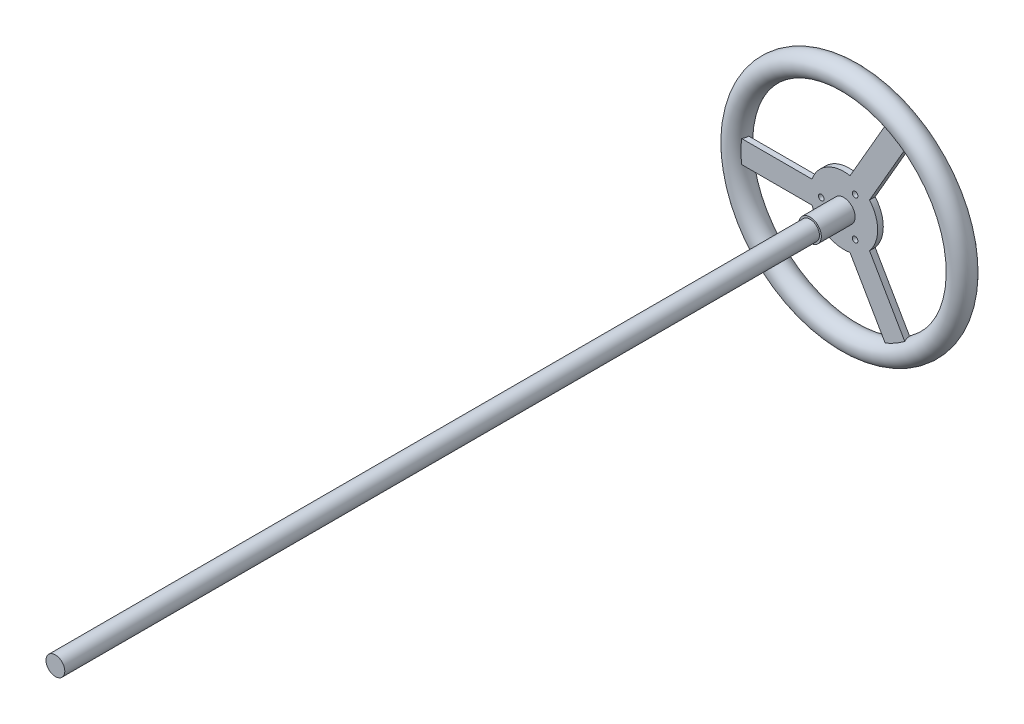
SolidWorks part; units mm, degrees
ref_plane "Front Plane" through (0, 0, 0) normal (0, 0, 1) x (1, 0, 0)
ref_plane "Top Plane" through (0, 0, 0) normal (0, 1, 0) x (1, 0, 0)
ref_plane "Right Plane" through (0, 0, 0) normal (1, 0, 0) x (0, 0, -1)
sketch "Sketch3" plane through (0, 0, 0) normal (0, 0, 1) x (1, 0, 0)
  circle A0 centre (0, 0) radius 30
  circle A1 centre (0, 0) radius 20 construction
  circle A2 centre (-20, 0) radius 2.5
  circle A3 centre (10, 17.3205) radius 2.5
  circle A4 centre (10, -17.3205) radius 2.5
  point P12 (0, 0)
  dimension "D1" = 60
  dimension "D2" = 3
extrude "Boss-Extrude1" add sketch "Sketch3" along normal blind 5
sketch "Sketch4" plane through (0, 0, 5) normal (0, 0, 1) x (1, 0, 0)
  circle A0 centre (0, 0) radius 8.35
extrude "Boss-Extrude2" add sketch "Sketch4" along normal blind 700
sketch "Sketch6" plane through (0, 0, 5) normal (0, 0, 1) x (1, 0, 0)
  circle A0 centre (0, 0) radius 10
extrude "Boss-Extrude3" add sketch "Sketch6" along normal blind 30
sketch "Sketch8" plane through (0, 0, 0) normal (0, 0, -1) x (-1, 0, 0)
  line L0 (-41.3397, -91.6025) -> (-5.3803, -29.319)
  line L1 (100, 10) -> (28.0811, 10)
  line L2 (100, -10) -> (28.0811, -10)
  line L3 (28.0811, 10) -> (100, 10)
  line L4 (28.0811, -10) -> (100, -10)
  line L5 (-99.4987, -10) -> (-100, -10)
  line L6 (-58.6603, -81.6025) -> (-22.7008, -19.319)
  line L7 (-58.6603, 81.6025) -> (-22.7008, 19.319)
  line L8 (-99.4987, 10) -> (-100, 10)
  line L10 (-41.3397, 91.6025) -> (-5.3803, 29.319)
  circle A0 centre (0, 0) radius 100
  circle A1 centre (0, 0) radius 29.8086
  point P9 (28.0811, 10)
  point P10 (28.0811, -10)
  point P24 (0, 0)
  circle M2 centre (0, 0) radius 30
  dimension "D1" = 3
extrude "Boss-Extrude4" add sketch "Sketch8" against normal up to surface (5 mm away) contours L10 A0 L7 M2 | L4 A0 L3 M2 | L6 A0 L0 M2 up to face at (12.5, 17.3205, 5)
sketch "Sketch10" plane through (0, 0, 0) normal (0, 0, -1) x (-1, 0, 0)
  circle A0 centre (0, 0) radius 100
sketch "Sketch11" plane through (0, 0, 0) normal (0, 1, 0) x (1, 0, 0)
  line L0 (100, 0) -> (-100, 0) construction
  circle A0 centre (100, 0) radius 10
  dimension "D1" = 20
sweep "Sweep1" add profiles "Sketch11" path "Sketch10"
